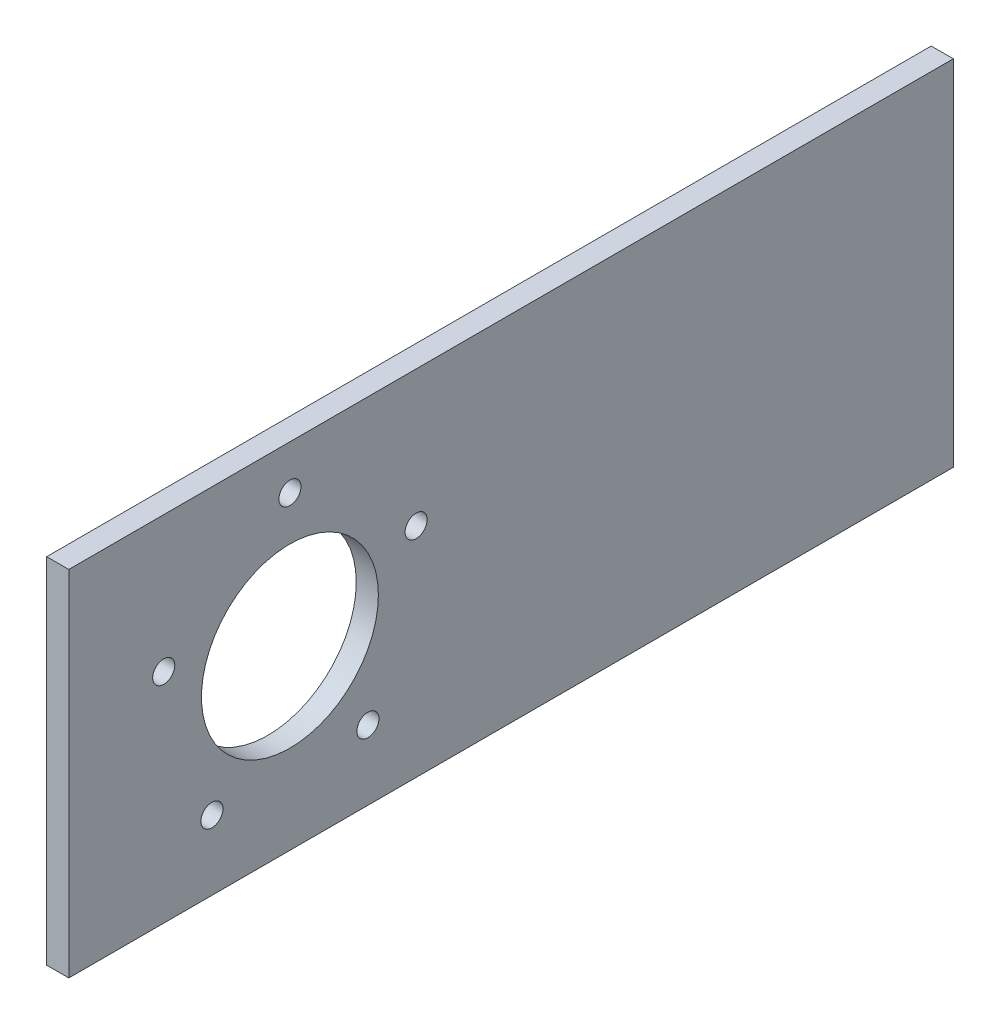
SolidWorks part; units mm, degrees
ref_plane "Front Plane" through (0, 0, 0) normal (0, 0, 1) x (1, 0, 0)
ref_plane "Top Plane" through (0, 0, 0) normal (0, 1, 0) x (1, 0, 0)
ref_plane "Right Plane" through (0, 0, 0) normal (1, 0, 0) x (0, 0, -1)
sketch "Sketch1" plane through (0, 0, 0) normal (1, 0, 0) x (0, 0, -1)
  line L0 (3.4925, 0) -> (-3.4925, 0) construction
  line L1 (-127, 50.8) -> (127, 50.8)
  line L2 (-127, 50.8) -> (-127, -50.8)
  line L3 (-127, -50.8) -> (127, -50.8)
  line L4 (127, 50.8) -> (127, -50.8)
  line L5 (-127, 50.8) -> (127, -50.8) construction
  line L6 (-127, -50.8) -> (127, 50.8) construction
  circle A0 centre (-63.5, 0) radius 25.4
  point P0 (0, 0)
  dimension "D3" = 50.8
  dimension "D1" = 101.6
  dimension "D2" = 254
  dimension "D4" = 63.5
extrude "Boss-Extrude1" add sketch "Sketch1" along normal mid plane 6.35
sketch "Sketch2" plane through (3.175, 0, 0) normal (1, 0, 0) x (0, 0, -1)
  line L0 (-127, 50.8) -> (-127, -50.8) construction
  line L1 (3.4925, 0) -> (-3.4925, 0) construction
  circle A0 centre (-63.5, 38.1) radius 3.175
  dimension "D3" = 6.35
  dimension "D1" = 63.5
  dimension "D2" = 38.1
extrude "Cut-Extrude1" cut sketch "Sketch2" against normal through all
pattern_circular "CirPattern1" count 5 over 360 about axis through (0, 0, 63.5) along (1, 0, 0) of "Cut-Extrude1"
